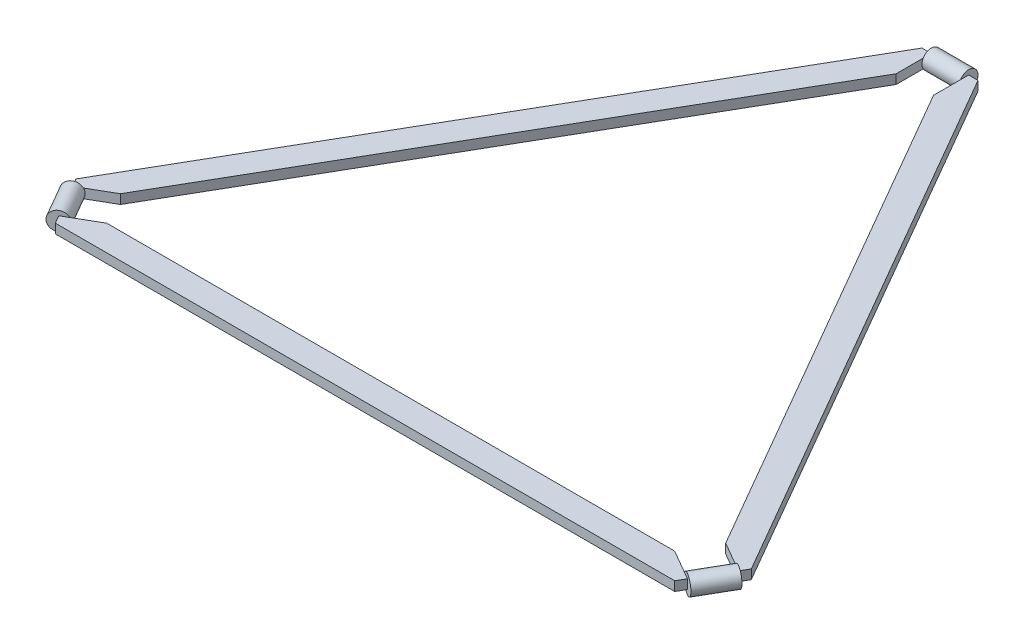
SolidWorks part; units mm, degrees
ref_plane "Alzado" through (0, 0, 0) normal (0, 0, 1) x (1, 0, 0)
ref_plane "Planta" through (0, 0, 0) normal (0, 1, 0) x (1, 0, 0)
ref_plane "Vista lateral" through (0, 0, 0) normal (1, 0, 0) x (0, 0, -1)
sketch "Croquis4" plane through (0, 0, 0) normal (0, 1, 0) x (1, 0, 0)
  line L0 (0, 400) -> (0, 0) construction
  line L1 (346.4102, -200) -> (0, 0) construction
  line L2 (-346.4102, -200) -> (0, 0) construction
  line L3 (-30, 400) -> (30, 400)
  line L4 (361.4102, -174.0192) -> (331.4102, -225.9808)
  line L5 (-331.4102, -225.9808) -> (-361.4102, -174.0192)
  line L6 (-30, 400) -> (-361.4102, -174.0192)
  line L7 (361.4102, -174.0192) -> (30, 400)
  line L8 (331.4102, -225.9808) -> (-331.4102, -225.9808)
  line L21 (-20, 400) -> (20, 400) construction
  line L22 (356.4102, -182.6795) -> (336.4102, -217.3205) construction
  line L23 (-336.4102, -217.3205) -> (-356.4102, -182.6795) construction
  line L24 (-20, 400) -> (-20, 362.3987)
  line L25 (-20, 362.3987) -> (-323.8465, -163.8789)
  line L26 (-323.8465, -163.8789) -> (-356.4102, -182.6795)
  line L27 (356.4102, -182.6795) -> (323.8465, -163.8789)
  line L28 (323.8465, -163.8789) -> (20, 362.3987)
  line L29 (20, 362.3987) -> (20, 400)
  line L30 (-336.4102, -217.3205) -> (-303.8465, -198.5199)
  line L31 (-303.8465, -198.5199) -> (303.8465, -198.5199)
  line L32 (303.8465, -198.5199) -> (336.4102, -217.3205)
  circle A0 centre (0, 0) radius 400 construction
  point P8 (0, 0)
  point P10 (0, 400)
  point P16 (0, 0)
  point P18 (0, 400)
  point P24 (0, 0)
  point P35 (0, 0)
  dimension "D1" = 400
  dimension "D3" = 60
  dimension "D5" = 40
  dimension "D7" = 27.4609
  dimension "D2" = 3
  dimension "D4" = 3
  dimension "D6" = 3
  dimension "D8" = 3
extrude "Saliente-Extruir2" add sketch "Croquis4" along normal mid plane 10 contours L32 L31 L30 L5 L8 L4 | L26 L25 L24 L3 L6 L5 | L29 L28 L27 L4 L7 L3
sketch "Croquis5" plane through (0, 0, 0) normal (1, 0, 0) x (0, 0, -1)
  circle A0 centre (400, 0) radius 10
  dimension "D1" = 20
extrude "Saliente-Extruir3" add sketch "Croquis5" along normal up to surface (40 mm away) from surface at -20 up to face at (20, 0, -381.1994) starting at face at (-20, 0, -381.1994)
sketch "Croquis6" plane through (-10, 0, -17.3205) normal (0.5, 0, 0.866) x (0.866, 0, -0.5)
  line L0 (174.0192, 0) -> (-400, 0) construction
  line L1 (400, 0) -> (-400, 0) construction
  line L2 (-362.3987, 0) -> (-400, 0) construction
  circle A0 centre (-400, 0) radius 10
  dimension "D1" = 20
extrude "Saliente-Extruir4" add sketch "Croquis6" along normal up to surface (40 mm away) up to face at (-320.1283, 0, 207.9202)
sketch "Croquis7" plane through (10, 0, -17.3205) normal (-0.5, 0, 0.866) x (0.866, 0, 0.5)
  line L0 (400, 0) -> (-174.0192, 0) construction
  line L1 (400, 0) -> (362.3987, 0) construction
  circle A0 centre (400, 0) radius 10
  dimension "D1" = 20
extrude "Saliente-Extruir5" add sketch "Croquis7" along normal up to surface (40 mm away) up to face at (320.1283, 0, 207.9202)
